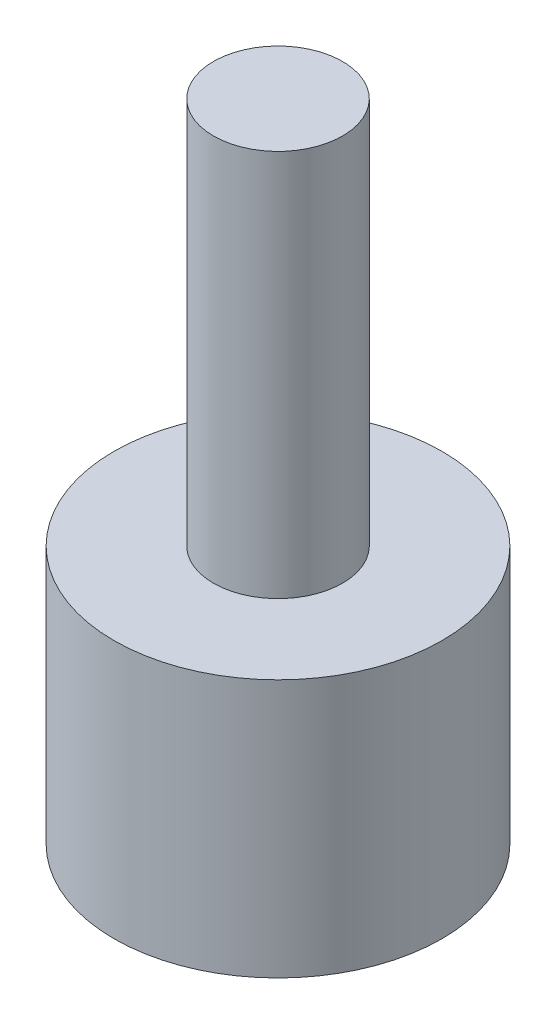
SolidWorks part; units mm, degrees
ref_plane "Front Plane" through (0, 0, 0) normal (0, 0, 1) x (1, 0, 0)
ref_plane "Top Plane" through (0, 0, 0) normal (0, 1, 0) x (1, 0, 0)
ref_plane "Right Plane" through (0, 0, 0) normal (1, 0, 0) x (0, 0, -1)
sketch "Sketch1" plane through (0, 0, 0) normal (0, 1, 0) x (1, 0, 0)
  circle A0 centre (0, 0) radius 6.35
  dimension "D1" = 12.7
extrude "Boss-Extrude1" add sketch "Sketch1" along normal blind 10
sketch "Sketch2" plane through (0, 10, 0) normal (0, 1, 0) x (1, 0, 0)
  circle A0 centre (0, 0) radius 2.5
  dimension "D1" = 5
extrude "Boss-Extrude2" add sketch "Sketch2" along normal blind 15
